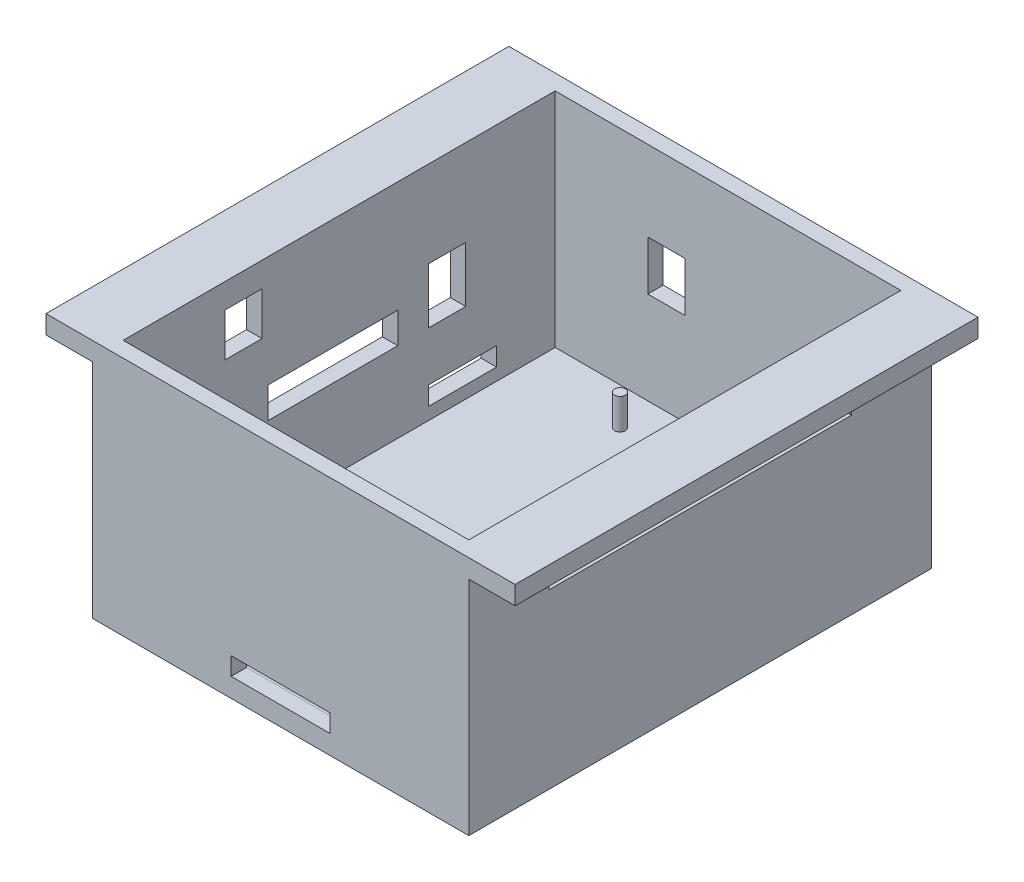
SolidWorks part; units mm, degrees
ref_plane "Front Plane" through (0, 0, 0) normal (0, 0, 1) x (1, 0, 0)
ref_plane "Top Plane" through (0, 0, 0) normal (0, 1, 0) x (1, 0, 0)
ref_plane "Right Plane" through (0, 0, 0) normal (1, 0, 0) x (0, 0, -1)
sketch "Sketch1" plane through (0, 0, 0) normal (0, 0, 1) x (1, 0, 0)
  line L0 (-37.7714, 7.6901) -> (-37.7714, 10.6901)
  line L1 (-37.7714, 10.6901) -> (38.2286, 10.6901)
  line L2 (38.2286, 10.6901) -> (38.2286, 7.6901)
  line L3 (38.2286, 7.6901) -> (30.7286, 7.6901)
  line L4 (30.7286, 7.6901) -> (30.7286, -28.3099)
  line L5 (30.7286, -28.3099) -> (-30.2714, -28.3099)
  line L6 (-30.2714, -28.3099) -> (-30.2714, 7.6901)
  line L7 (-30.2714, 7.6901) -> (-37.7714, 7.6901)
  dimension "D1" = 61
  dimension "D2" = 76
  dimension "D3" = 7.5
  dimension "D4" = 3
  dimension "D5" = 3
  dimension "D6" = 7.5
  dimension "D7" = 36
extrude "Boss-Extrude1" add sketch "Sketch1" along normal blind 75
sketch "Sketch4" plane through (0, 10.6901, 0) normal (0, 1, 0) x (1, 0, 0)
  line L0 (-37.7714, -37.5) -> (38.2286, -37.5) construction
  line L1 (-37.7714, -75) -> (-37.7714, 0) construction
  line L2 (38.2286, -75) -> (38.2286, 0) construction
  line L3 (38.2286, 0) -> (-37.7714, 0) construction
  line L4 (0.2286, 0) -> (0.2286, -75) construction
  line L5 (38.2286, -75) -> (-37.7714, -75) construction
  line L7 (-27.7714, -2.5) -> (28.2286, -2.5)
  line L8 (-27.7714, -2.5) -> (-27.7714, -72.5)
  line L9 (-27.7714, -72.5) -> (28.2286, -72.5)
  line L10 (28.2286, -2.5) -> (28.2286, -72.5)
  line L11 (-27.7714, -2.5) -> (28.2286, -72.5) construction
  line L12 (-27.7714, -72.5) -> (28.2286, -2.5) construction
  point P12 (0.2286, -37.5)
  dimension "D1" = 56
  dimension "D2" = 70
extrude "Cut-Extrude1" cut sketch "Sketch4" against normal blind 36
sketch "Sketch20" plane through (0, -25.3099, 0) normal (0, 1, 0) x (1, 0, 0)
  line L0 (0.2286, -2.5) -> (0.2286, -72.5) construction
  line L1 (28.2286, -2.5) -> (-27.7714, -2.5) construction
  line L2 (-27.7714, -72.5) -> (28.2286, -72.5) construction
  line L4 (11.7286, -8.5) -> (-11.2714, -8.5)
  line L5 (11.7286, -8.5) -> (11.7286, -66.5)
  line L6 (11.7286, -66.5) -> (-11.2714, -66.5)
  line L7 (-11.2714, -8.5) -> (-11.2714, -66.5)
  line L8 (0.2286, -66.5) -> (0.2286, -8.5) construction
  line L9 (11.7286, -37.5) -> (-11.2714, -37.5) construction
  point P6 (0.2286, -37.5)
  dimension "D1" = 58
  dimension "D2" = 23
sketch "Sketch21" plane through (0, -25.3099, 0) normal (0, 1, 0) x (1, 0, 0)
  circle A0 centre (-11.2714, -8.5) radius 0.875
  circle A1 centre (11.7286, -8.5) radius 0.875
  circle A2 centre (-11.2714, -66.5) radius 0.875
  circle A3 centre (11.7286, -66.5) radius 0.875
  dimension "D1" = 1.75
  dimension "D2" = 1.75
  dimension "D3" = 1.75
  dimension "D4" = 1.75
extrude "Boss-Extrude3" add sketch "Sketch21" along normal blind 5
sketch "Sketch23" plane through (0, 0, 0) normal (0, 0, -1) x (-1, 0, 0)
  line L0 (-30.7286, -28.3099) -> (-30.7286, 7.6901) construction
  line L1 (-8.0286, -22.3099) -> (3.8714, -22.3099)
  line L2 (-8.0286, -22.3099) -> (-8.0286, -25.2099)
  line L3 (-8.0286, -25.2099) -> (3.8714, -25.2099)
  line L4 (3.8714, -22.3099) -> (3.8714, -25.2099)
  line L5 (30.2714, -28.3099) -> (-30.7286, -28.3099) construction
  dimension "D1" = 22.7
  dimension "D2" = 34.6
  dimension "D3" = 3.1
  dimension "D4" = 6
extrude "Cut-Extrude2" cut sketch "Sketch23" against normal up to next
sketch "Sketch24" plane through (-30.2714, 0, 0) normal (-1, 0, 0) x (0, 0, 1)
  line L0 (0, 7.6901) -> (0, -28.3099) construction
  line L1 (12, -20.3099) -> (23, -20.3099)
  line L2 (12, -20.3099) -> (12, -23.3099)
  line L3 (12, -23.3099) -> (23, -23.3099)
  line L4 (23, -20.3099) -> (23, -23.3099)
  line L5 (75, -28.3099) -> (0, -28.3099) construction
  dimension "D1" = 12
  dimension "D2" = 23
  dimension "D3" = 5
  dimension "D4" = 8
extrude "Cut-Extrude3" cut sketch "Sketch24" against normal up to next
sketch "Sketch25" plane through (-30.2714, 0, 0) normal (-1, 0, 0) x (0, 0, 1)
  line L0 (75, 7.6901) -> (75, -28.3099) construction
  line L1 (42.9, -21.3099) -> (49.9, -21.3099)
  line L2 (42.9, -21.3099) -> (42.9, -23.3099)
  line L3 (42.9, -23.3099) -> (49.9, -23.3099)
  line L4 (49.9, -21.3099) -> (49.9, -23.3099)
  line L5 (75, -28.3099) -> (0, -28.3099) construction
  dimension "D1" = 25.1
  dimension "D2" = 32.1
  dimension "D3" = 7
  dimension "D4" = 5
extrude "Cut-Extrude4" cut sketch "Sketch25" against normal up to next
sketch "Sketch26" plane through (-30.2714, 0, 0) normal (-1, 0, 0) x (0, 0, 1)
  line L0 (75, 7.6901) -> (75, -28.3099) construction
  line L1 (55.8, -21.3099) -> (63, -21.3099)
  line L2 (55.8, -21.3099) -> (55.8, -23.3099)
  line L3 (55.8, -23.3099) -> (63, -23.3099)
  line L4 (63, -21.3099) -> (63, -23.3099)
  line L5 (75, -28.3099) -> (0, -28.3099) construction
  dimension "D1" = 12
  dimension "D2" = 19.2
  dimension "D3" = 5
  dimension "D4" = 7
extrude "Cut-Extrude5" cut sketch "Sketch26" against normal up to next
sketch "Sketch27" plane through (0, 0, 75) normal (0, 0, 1) x (1, 0, 0)
  line L0 (-30.2714, 7.6901) -> (-30.2714, -28.3099) construction
  line L1 (-7.7714, -22.3099) -> (8.2286, -22.3099)
  line L2 (-7.7714, -22.3099) -> (-7.7714, -25.2099)
  line L3 (-7.7714, -25.2099) -> (8.2286, -25.2099)
  line L4 (8.2286, -22.3099) -> (8.2286, -25.2099)
  line L5 (30.7286, -28.3099) -> (30.7286, 7.6901) construction
  line L6 (-30.2714, -28.3099) -> (30.7286, -28.3099) construction
  dimension "D1" = 22.5
  dimension "D2" = 22.5
  dimension "D3" = 3.1
  dimension "D4" = 6
extrude "Cut-Extrude6" cut sketch "Sketch27" against normal up to next
sketch "Sketch28" plane through (-30.2714, 0, 0) normal (-1, 0, 0) x (0, 0, 1)
  line L0 (0, 7.6901) -> (0, -28.3099) construction
  line L1 (17, -3.3099) -> (23, -3.3099)
  line L2 (17, -3.3099) -> (17, -12.3099)
  line L3 (17, -12.3099) -> (23, -12.3099)
  line L4 (23, -3.3099) -> (23, -12.3099)
  line L5 (75, -28.3099) -> (0, -28.3099) construction
  dimension "D1" = 17
  dimension "D2" = 23
  dimension "D3" = 25
  dimension "D4" = 16
extrude "Cut-Extrude7" cut sketch "Sketch28" against normal up to next
sketch "Sketch29" plane through (-30.2714, 0, 0) normal (-1, 0, 0) x (0, 0, 1)
  line L0 (0, 7.6901) -> (0, -28.3099) construction
  line L1 (28, -7.3099) -> (49, -7.3099)
  line L2 (28, -7.3099) -> (28, -12.3099)
  line L3 (28, -12.3099) -> (49, -12.3099)
  line L4 (49, -7.3099) -> (49, -12.3099)
  line L5 (75, -28.3099) -> (0, -28.3099) construction
  dimension "D1" = 28
  dimension "D2" = 49
  dimension "D3" = 16
  dimension "D4" = 21
extrude "Cut-Extrude8" cut sketch "Sketch29" against normal up to next
sketch "Sketch30" plane through (0, 0, 0) normal (0, 0, -1) x (-1, 0, 0)
  line L0 (30.2714, -28.3099) -> (-30.7286, -28.3099) construction
  line L1 (6.7714, -2.3099) -> (12.7714, -2.3099)
  line L2 (6.7714, -2.3099) -> (6.7714, -10.3099)
  line L3 (6.7714, -10.3099) -> (12.7714, -10.3099)
  line L4 (12.7714, -2.3099) -> (12.7714, -10.3099)
  line L5 (30.2714, 7.6901) -> (30.2714, -28.3099) construction
  dimension "D1" = 18
  dimension "D2" = 26
  dimension "D3" = 23.5
  dimension "D4" = 17.5
extrude "Cut-Extrude9" cut sketch "Sketch30" against normal up to next
sketch "Sketch31" plane through (30.7286, 0, 0) normal (1, 0, 0) x (0, 0, -1)
  line L0 (-75, -28.3099) -> (-75, 7.6901) construction
  line L1 (-62, 6.6901) -> (-13, 6.6901)
  line L2 (-62, 6.6901) -> (-62, -0.3099)
  line L3 (-62, -0.3099) -> (-13, -0.3099)
  line L4 (-13, 6.6901) -> (-13, -0.3099)
  line L5 (0, -28.3099) -> (0, 7.6901) construction
  line L6 (-75, -28.3099) -> (0, -28.3099) construction
  dimension "D1" = 13
  dimension "D2" = 13
  dimension "D3" = 35
  dimension "D4" = 28
extrude "Cut-Extrude10" cut sketch "Sketch31" against normal up to next
sketch "Sketch32" plane through (-30.2714, 0, 0) normal (-1, 0, 0) x (0, 0, 1)
  line L0 (75, -28.3099) -> (0, -28.3099) construction
  line L1 (50, 6.6901) -> (56, 6.6901)
  line L2 (50, 6.6901) -> (50, -0.3099)
  line L3 (50, -0.3099) -> (56, -0.3099)
  line L4 (56, 6.6901) -> (56, -0.3099)
  line L5 (75, 7.6901) -> (75, -28.3099) construction
  dimension "D1" = 35
  dimension "D2" = 28
  dimension "D3" = 25
  dimension "D4" = 19
extrude "Cut-Extrude11" cut sketch "Sketch32" against normal up to next
